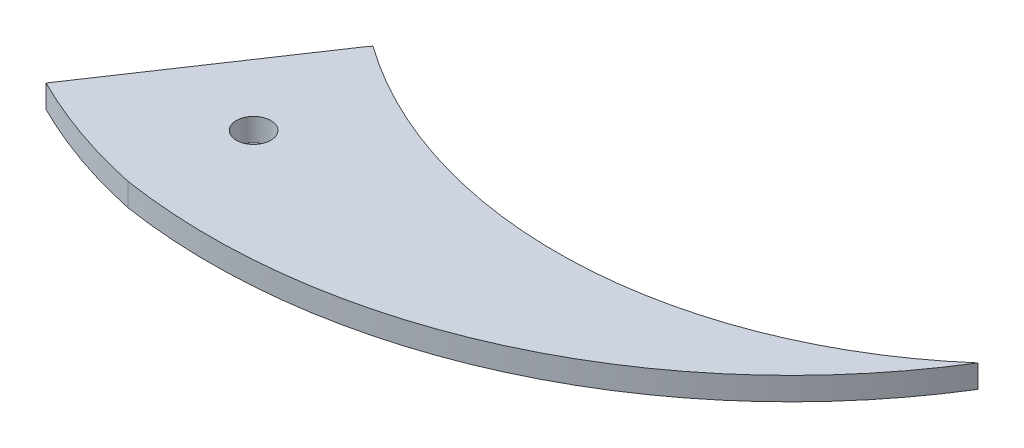
SolidWorks part; units mm, degrees
material "Stainless Steel (ferritic)"
ref_plane "Front Plane" through (0, 0, 0) normal (0, 0, 1) x (1, 0, 0)
ref_plane "Top Plane" through (0, 0, 0) normal (0, 1, 0) x (1, 0, 0)
ref_plane "Right Plane" through (0, 0, 0) normal (1, 0, 0) x (0, 0, -1)
sketch "Sketch4" plane through (0, 0, 0) normal (0, 1, 0) x (1, 0, 0)
  line L0 (-19.2537, -12.6558) -> (-13.6823, -4.3516)
  arc A0 (-19.2537, -12.6558) -> (-13.7652, -14.5784) centre (-8.9121, 8.0707) ccw
  arc A1 (-13.5182, -4.1344) -> (11.6363, -2.9053) centre (-1.7182, 12.3884) ccw
  arc A4 (-13.6823, -4.3516) -> (-13.5182, -4.1344) centre (-22.9252, 2.8014) ccw
  arc A6 (11.6363, -2.9053) -> (-13.7652, -14.5784) centre (-9.8821, 10.446) cw
  dimension "D1" = 10
extrude "Boss-Extrude2" add sketch "Sketch4" along normal blind 1
sketch "Sketch6" plane through (0, 1, 0) normal (0, 1, 0) x (1, 0, 0)
  circle A0 centre (-12.9374, -9.9199) radius 0.75
  dimension "D1" = 1.5
extrude "Cut-Extrude3" cut sketch "Sketch6" against normal blind 10
